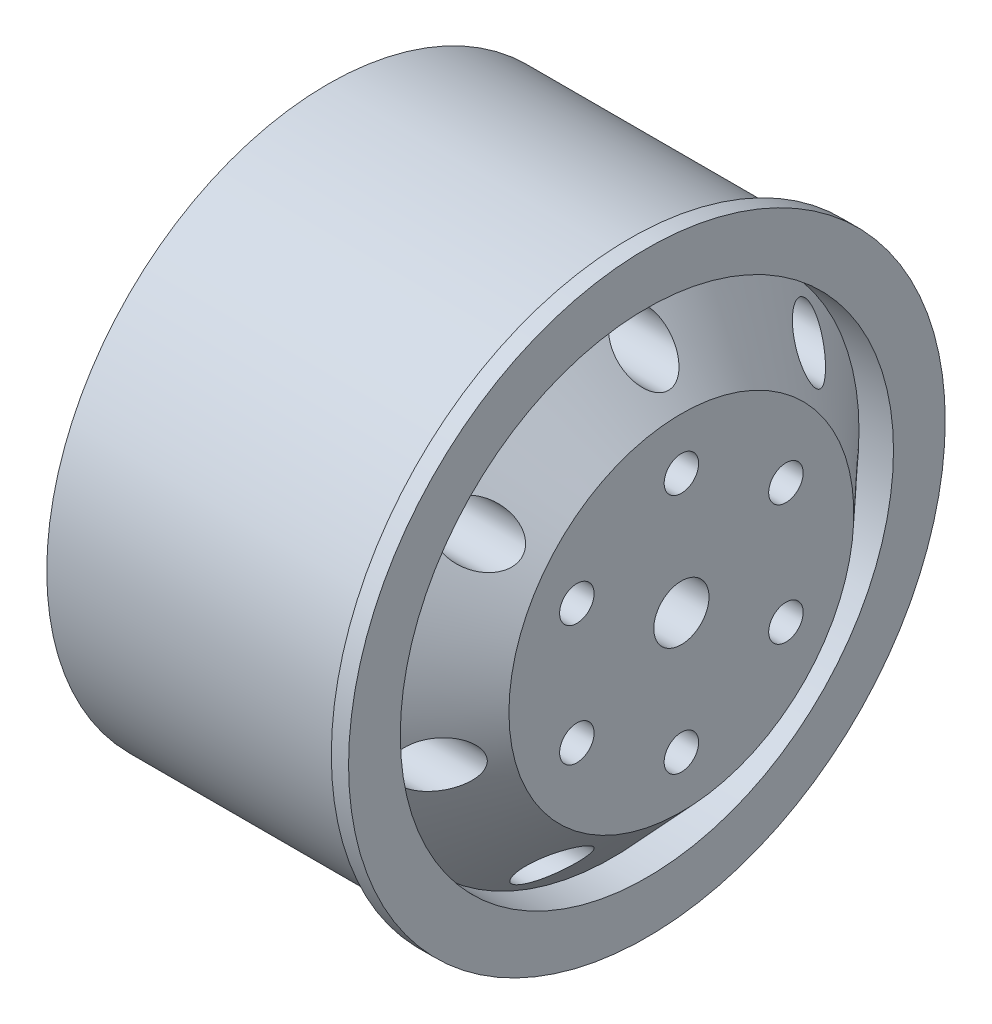
SolidWorks part; units mm, degrees
ref_plane "Front Plane" through (0, 0, 0) normal (0, 0, 1) x (1, 0, 0)
ref_plane "Top Plane" through (0, 0, 0) normal (0, 1, 0) x (1, 0, 0)
ref_plane "Right Plane" through (0, 0, 0) normal (1, 0, 0) x (0, 0, -1)
sketch "Sketch1" plane through (0, 0, 0) normal (0, 1, 0) x (1, 0, 0)
  line L0 (-9.0756, 0) -> (13.0084, 0) construction
  line L3 (7.5168, 16.3) -> (-9.9832, 16.3)
  line L5 (8.5168, 16.3) -> (8.5168, 14.3)
  line L6 (8.5168, 14.3) -> (6.5168, 14.3)
  line L8 (-9.9832, 16.3) -> (-9.9832, 13.3)
  line L9 (10.5168, 10) -> (10.5168, 0)
  line L10 (-9.9832, 13.3) -> (3.0684, 13.6024)
  line L13 (7.5168, 0) -> (10.5168, 0)
  line L14 (6.5168, 14.3) -> (10.5168, 10)
  line L15 (3.0684, 13.6024) -> (7.5168, 8.8204)
  line L16 (7.5168, 8.8204) -> (7.5168, 0)
  line L17 (8.5168, 16.3) -> (8.5168, 17.3)
  line L18 (8.5168, 17.3) -> (7.5168, 17.3)
  line L19 (7.5168, 17.3) -> (7.5168, 16.3)
  dimension "D1" = 18.5
  dimension "D2" = 32.6
  dimension "D3" = 2
  dimension "D4" = 2
  dimension "D5" = 20
  dimension "D6" = 3
  dimension "D7" = 3
  dimension "D8" = 3
  dimension "D9" = 1
  dimension "D10" = 1
revolve "Revolve1" add sketch "Sketch1" angle 360 about L0
sketch "Sketch2" plane through (10.5168, 0, 0) normal (1, 0, 0) x (0, 0, -1)
  circle A0 centre (0, 0) radius 1.6
  circle A2 centre (0, 7) radius 1
  circle A3 centre (0, 0) radius 7
  circle A4 centre (0, 0) radius 7 construction
  circle A5 centre (6.0622, 3.5) radius 1
  circle A6 centre (6.0622, -3.5) radius 1
  circle A7 centre (0, -7) radius 1
  circle A8 centre (-6.0622, -3.5) radius 1
  circle A9 centre (-6.0622, 3.5) radius 1
  circle A11 centre (0, 12.3) radius 1.5
  circle A12 centre (0, 0) radius 12.3
  circle A13 centre (0, 0) radius 12.3 construction
  circle A14 centre (9.6165, 7.6689) radius 1.5
  circle A15 centre (11.9916, -2.737) radius 1.5
  circle A16 centre (5.3368, -11.0819) radius 1.5
  circle A17 centre (-5.3368, -11.0819) radius 1.5
  circle A18 centre (-11.9916, -2.737) radius 1.5
  circle A19 centre (-9.6165, 7.6689) radius 1.5
  point P21 (0, 0)
  point P39 (0, 0)
  dimension "D1" = 3.2
  dimension "D3" = 2
  dimension "D6" = 3
  dimension "D2" = 3
  dimension "D5" = 2
  dimension "D4" = 6
  dimension "D7" = 7
extrude "Cut-Extrude2" cut sketch "Sketch2" against normal blind 8
